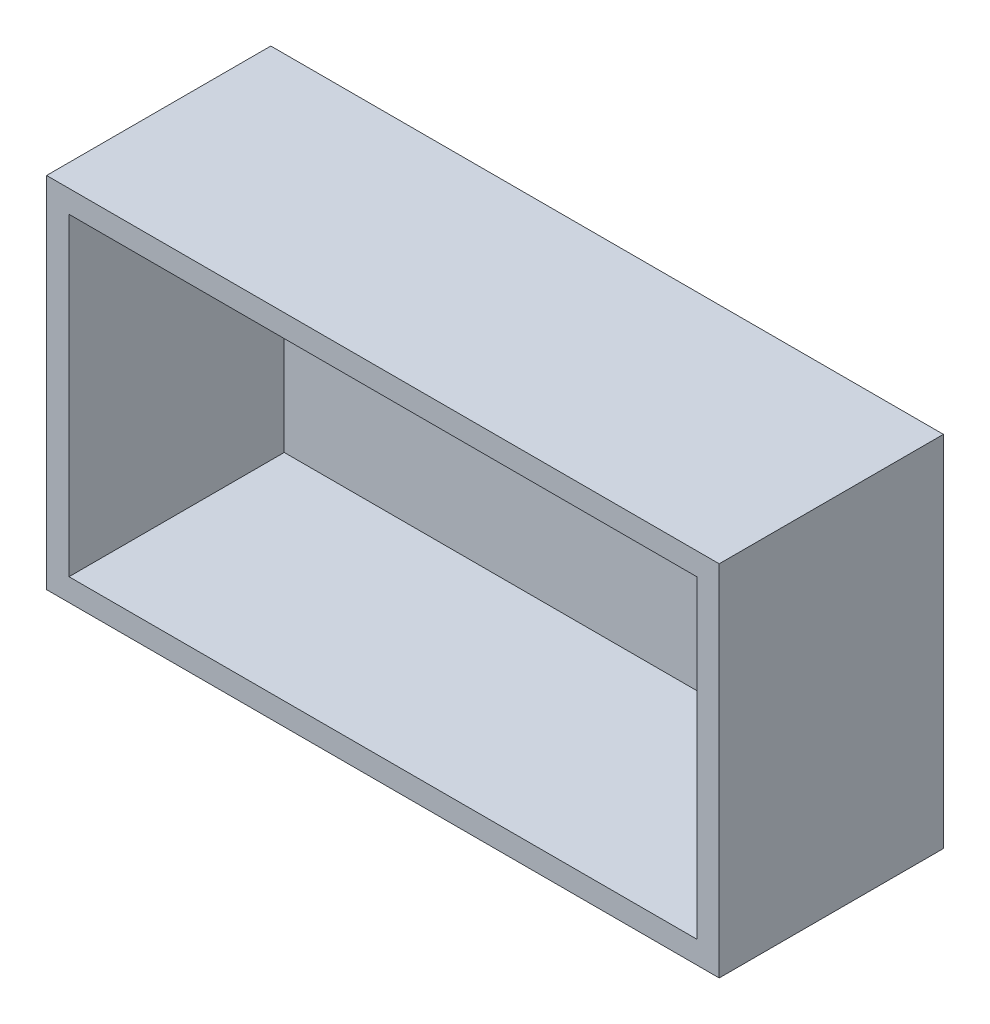
SolidWorks part; units mm, degrees
ref_plane "Front Plane" through (0, 0, 0) normal (0, 0, 1) x (1, 0, 0)
ref_plane "Top Plane" through (0, 0, 0) normal (0, 1, 0) x (1, 0, 0)
ref_plane "Right Plane" through (0, 0, 0) normal (1, 0, 0) x (0, 0, -1)
sketch "Sketch1" plane through (0, 0, 0) normal (0, 0, 1) x (1, 0, 0)
  line L1 (-78.9557, 10.1266) -> (71.0443, 10.1266)
  line L2 (-78.9557, 10.1266) -> (-78.9557, -69.8734)
  line L3 (-78.9557, -69.8734) -> (71.0443, -69.8734)
  line L4 (71.0443, 10.1266) -> (71.0443, -69.8734)
  dimension "D1" = 150
  dimension "D2" = 80
extrude "Boss-Extrude1" add sketch "Sketch1" along normal blind 50
sketch "Sketch2" plane through (0, 0, 50) normal (0, 0, 1) x (1, 0, 0)
  line L0 (71.0443, -69.8734) -> (71.0443, 10.1266) construction
  line L1 (66.0443, -64.8734) -> (-73.9557, -64.8734)
  line L2 (66.0443, -64.8734) -> (66.0443, 5.1266)
  line L3 (66.0443, 5.1266) -> (-73.9557, 5.1266)
  line L4 (-73.9557, -64.8734) -> (-73.9557, 5.1266)
  line L5 (-78.9557, 10.1266) -> (-78.9557, -69.8734) construction
  line L6 (-78.9557, -69.8734) -> (71.0443, -69.8734) construction
  line L7 (71.0443, 10.1266) -> (-78.9557, 10.1266) construction
  dimension "D1" = 5
  dimension "D2" = 5
  dimension "D3" = 5
  dimension "D4" = 5
extrude "Cut-Extrude1" cut sketch "Sketch2" against normal blind 48
